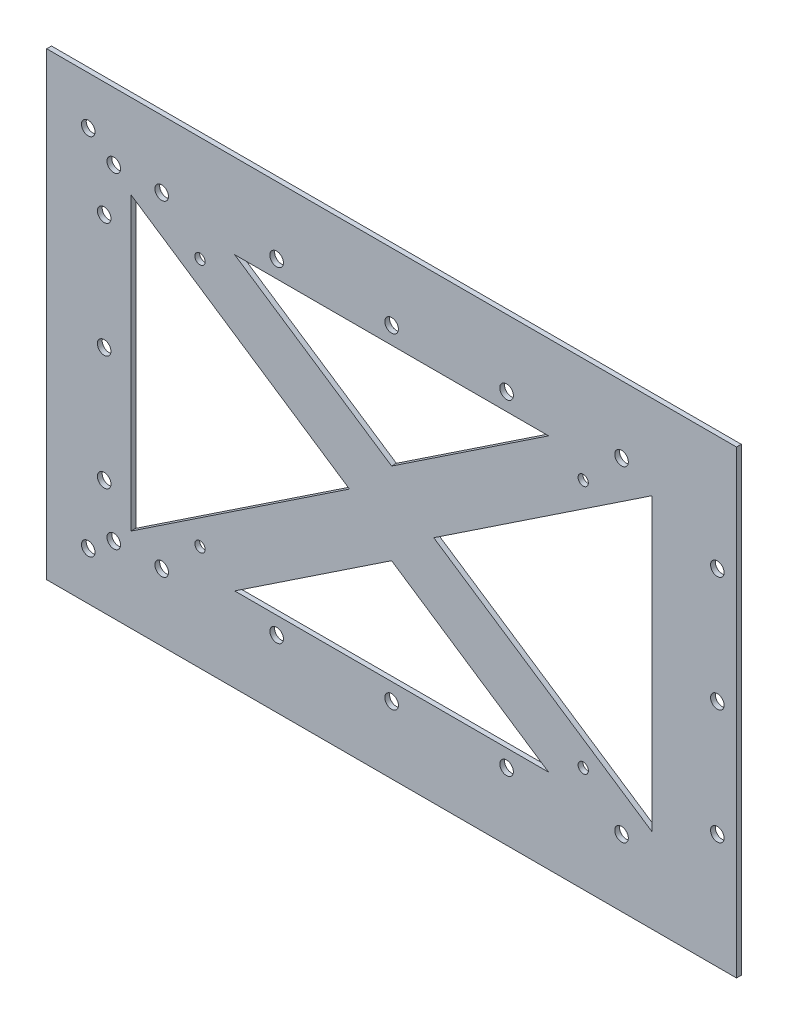
SolidWorks part; units mm, degrees
ref_plane "Front Plane" through (0, 0, 0) normal (0, 0, 1) x (1, 0, 0)
ref_plane "Top Plane" through (0, 0, 0) normal (0, 1, 0) x (1, 0, 0)
ref_plane "Right Plane" through (0, 0, 0) normal (1, 0, 0) x (0, 0, -1)
sketch "Sketch1" plane through (0, 0, 0) normal (0, 0, 1) x (1, 0, 0)
  line L0 (-52.0171, 48.26) -> (52.0171, 48.26)
  line L1 (-114.3, -76.2) -> (114.3, -76.2)
  line L2 (-114.3, -76.2) -> (-114.3, 76.2)
  line L3 (-114.3, 76.2) -> (114.3, 76.2)
  line L4 (114.3, -76.2) -> (114.3, 76.2)
  line L5 (-114.3, -76.2) -> (114.3, 76.2) construction
  line L6 (-114.3, 76.2) -> (114.3, -76.2) construction
  line L7 (52.0171, 48.26) -> (0, 13.5819)
  line L8 (0, 13.5819) -> (-52.0171, 48.26)
  line L9 (-86.36, 48.26) -> (-86.36, -48.26)
  line L10 (-86.36, -48.26) -> (-13.97, 0)
  line L11 (-13.97, 0) -> (-86.36, 48.26)
  line L12 (0, -13.5819) -> (-52.0171, -48.26)
  line L13 (-52.0171, -48.26) -> (52.0171, -48.26)
  line L14 (52.0171, -48.26) -> (0, -13.5819)
  line L15 (13.97, 0) -> (86.36, 48.26)
  line L16 (86.36, 48.26) -> (86.36, -48.26)
  line L17 (86.36, -48.26) -> (13.97, 0)
  point P0 (0, 0)
  dimension "D1" = 152.4
  dimension "D2" = 228.6
  dimension "D3" = 27.94
  dimension "D4" = 27.94
  dimension "D5" = 27.94
  dimension "D6" = 27.94
  dimension "D7" = 19.05
extrude "Boss-Extrude1" add sketch "Sketch1" along normal blind 1.5875
sketch "Sketch2" plane through (0, 0, 1.5875) normal (0, 0, 1) x (1, 0, 0)
  line L0 (-95.255, 38.1) -> (-95.255, 0) construction
  line L1 (-95.255, 0) -> (-95.255, -38.1) construction
  line L2 (-114.3, 76.2) -> (-114.3, -76.2) construction
  line L3 (114.3, 76.2) -> (-114.3, 76.2) construction
  line L4 (-114.3, -76.2) -> (114.3, -76.2) construction
  line L5 (114.3, -76.2) -> (114.3, 76.2) construction
  circle A0 centre (-100.5417, 60.325) radius 2.25
  circle A1 centre (-92.075, 53.975) radius 2.25
  circle A2 centre (-95.255, 38.1) radius 2.25
  circle A3 centre (-95.255, 0) radius 2.25
  circle A4 centre (-95.255, -38.1) radius 2.25
  circle A5 centre (-92.075, -53.975) radius 2.25
  circle A6 centre (-100.5417, -60.325) radius 2.25
  circle A7 centre (107.95, 38.1) radius 2.25
  circle A8 centre (107.95, 0) radius 2.25
  circle A9 centre (107.95, -38.1) radius 2.25
  circle A10 centre (-76.2, 53.975) radius 2.25
  circle A11 centre (-76.2, -53.975) radius 2.25
  circle A12 centre (-38.1, -53.975) radius 2.25
  circle A13 centre (-38.1, 53.975) radius 2.25
  circle A14 centre (0, -53.975) radius 2.25
  circle A15 centre (0, 53.975) radius 2.25
  circle A16 centre (38.1, -53.975) radius 2.25
  circle A17 centre (38.1, 53.975) radius 2.25
  circle A18 centre (76.2, -53.975) radius 2.25
  circle A19 centre (76.2, 53.975) radius 2.25
  dimension "D1" = 4.5
  dimension "D12" = 6.35
  dimension "D13" = 38.1
  dimension "D2" = 13.7583
  dimension "D3" = 15.875
  dimension "D4" = 6.35
  dimension "D5" = 8.4667
  dimension "D6" = 38.1
  dimension "D7" = 19.045
  dimension "D8" = 13.7583
  dimension "D9" = 15.875
  dimension "D10" = 8.4667
  dimension "D11" = 6.35
  dimension "D15" = 38.1
  dimension "D14" = 5
extrude "Cut-Extrude1" cut sketch "Sketch2" against normal through all
sketch "Sketch3" plane through (0, 0, 1.5875) normal (0, 0, 1) x (1, 0, 0)
  line L1 (-63.5, 41.275) -> (63.5, 41.275) construction
  line L2 (-63.5, 41.275) -> (-63.5, -41.275) construction
  line L3 (-63.5, -41.275) -> (63.5, -41.275) construction
  line L4 (63.5, 41.275) -> (63.5, -41.275) construction
  line L5 (-63.5, 41.275) -> (63.5, -41.275) construction
  line L6 (-63.5, -41.275) -> (63.5, 41.275) construction
  circle A0 centre (-63.5, 41.275) radius 1.7
  circle A1 centre (63.5, 41.275) radius 1.7
  circle A2 centre (-63.5, -41.275) radius 1.7
  circle A3 centre (63.5, -41.275) radius 1.7
  point P0 (0, 0)
  dimension "D3" = 3.4
  dimension "D1" = 82.55
  dimension "D2" = 127
extrude "Cut-Extrude2" cut sketch "Sketch3" against normal through all
